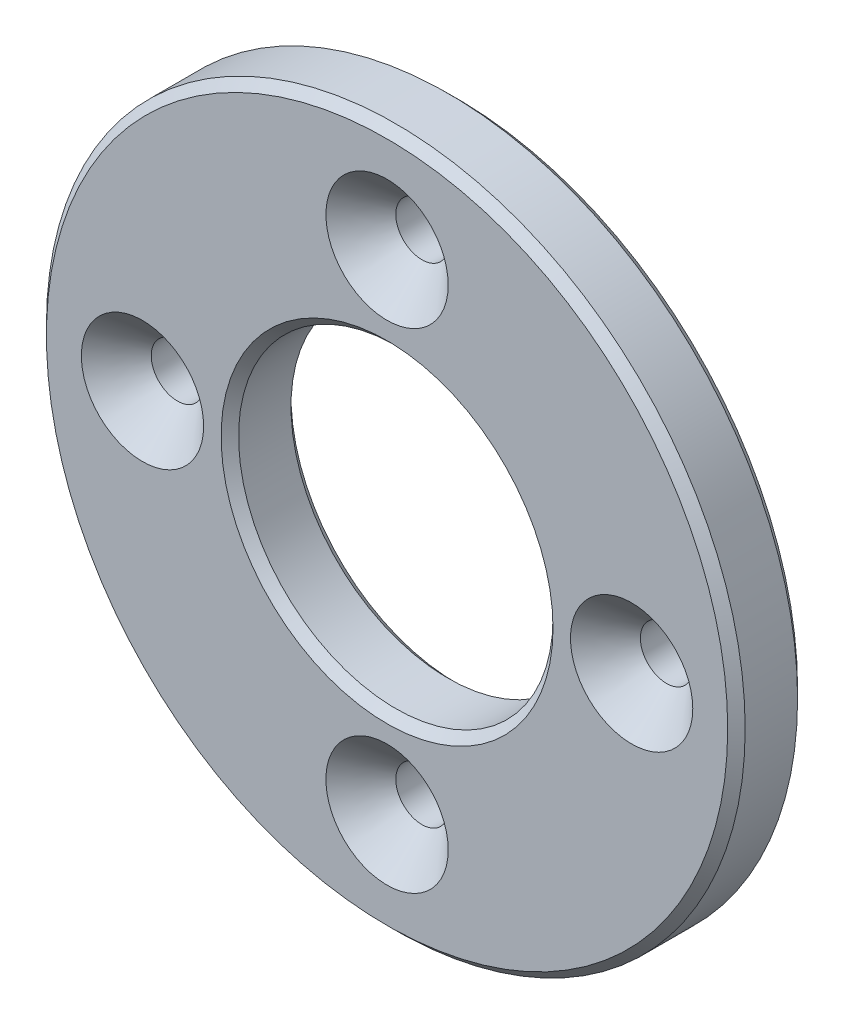
SolidWorks part; units mm, degrees
ref_plane "Face" through (0, 0, 0) normal (0, 0, 1) x (1, 0, 0)
ref_plane "Dessus" through (0, 0, 0) normal (0, 1, 0) x (1, 0, 0)
ref_plane "Droite" through (0, 0, 0) normal (1, 0, 0) x (0, 0, -1)
sketch "Esquisse1" plane through (0, 0, 0) normal (0, 0, 1) x (1, 0, 0)
  line L0 (0, 20) -> (0, -20) construction
  line L1 (-20, 0) -> (20, 0) construction
  line L2 (-14.1421, -14.1421) -> (14.1421, 14.1421) construction
  circle A0 centre (0, 0) radius 20
  circle A1 centre (0, 0) radius 9
  circle A2 centre (0, 14) radius 1.5
  circle A3 centre (-14, 0) radius 1.5
  circle A4 centre (14, 0) radius 1.5
  circle A5 centre (0, -14) radius 1.5
  dimension "D1" = 18
  dimension "D2" = 40
  dimension "D5" = 3
  dimension "D3" = 14
  dimension "D4" = 14
  dimension "D6" = 45
extrude "Extrusion1" add sketch "Esquisse1" along normal blind 4
chamfer "Chanfrein1" distance 2 angle 45 4 edges at (-1.5, -14, 4) (12.5, 0, 4) (1.5, 14, 4) (-12.5, 0, 4)
chamfer "Chanfrein2" distance 0.5 angle 45 4 edges at (9, 0, 0) (9, 0, 4) (20, 0, 0) (20, 0, 4)
